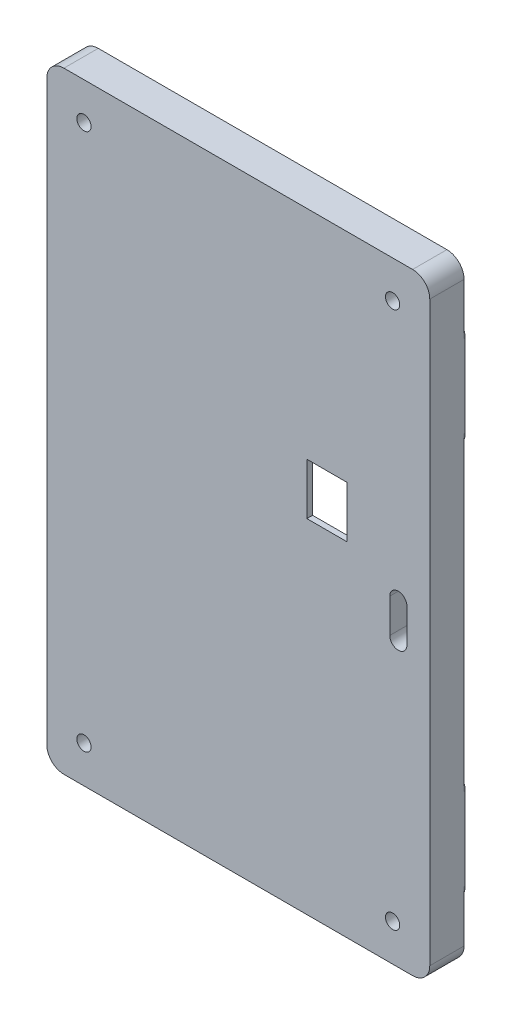
SolidWorks part; units mm, degrees
ref_plane "Přední rovina" through (0, 0, 0) normal (0, 0, 1) x (1, 0, 0)
ref_plane "Horní rovina" through (0, 0, 0) normal (0, 1, 0) x (1, 0, 0)
ref_plane "Pravá rovina" through (0, 0, 0) normal (1, 0, 0) x (0, 0, -1)
sketch "Skica1" plane through (0, 0, 0) normal (0, 0, 1) x (1, 0, 0)
  line L1 (0, 0) -> (67, 0)
  line L2 (0, 0) -> (0, 107)
  line L3 (0, 107) -> (67, 107)
  line L4 (67, 0) -> (67, 107)
  dimension "D1" = 67
  dimension "D2" = 107
extrude "Přidat vysunutím1" add sketch "Skica1" along normal blind 6
fillet "Zaoblit1" radius 3 4 edges at (67, 0, 3) (0, 0, 3) (0, 107, 3) (67, 107, 3)
sketch "Skica2" plane through (0, 0, 0) normal (0, 0, -1) x (-1, 0, 0)
  line L0 (-60.5, 100.5) -> (-6.5, 100.5) construction
  line L1 (-64, 107) -> (-3, 107) construction
  line L2 (-60.5, 100.5) -> (-60.5, 6.5) construction
  line L3 (-67, 3) -> (-67, 104) construction
  circle A0 centre (-6.5, 100.5) radius 1.25
  circle A1 centre (-60.5, 100.5) radius 1.25
  circle A2 centre (-6.5, 6.5) radius 1.25
  circle A3 centre (-60.5, 6.5) radius 1.25
  point P8 (-33.5, 100.5)
  point P11 (-33.5, 107)
  point P12 (-60.5, 53.5)
  point P15 (-67, 53.5)
  dimension "D3" = 2.5
  dimension "D4" = 2.5
  dimension "D5" = 2.5
  dimension "D6" = 2.5
  dimension "D1" = 94
  dimension "D2" = 54
extrude "Odebrat vysunutím1" cut sketch "Skica2" against normal through all
chamfer "Zkosení1" distance 1.25 angle 45 4 edges at (5.25, 6.5, 0) (59.25, 6.5, 0) (59.25, 100.5, 0) (5.25, 100.5, 0)
sketch "Skica4" plane through (0, 0, 0) normal (0, 0, -1) x (-1, 0, 0)
  line L0 (-61.5, 55.5) -> (-61.5, 49.55) construction
  line L1 (-52.5, 69) -> (-45.5, 69)
  line L2 (-52.5, 69) -> (-52.5, 60)
  line L3 (-52.5, 60) -> (-45.5, 60)
  line L4 (-45.5, 69) -> (-45.5, 60)
  line L5 (-60, 55.5) -> (-60, 49.55)
  line L6 (-63, 55.5) -> (-63, 49.55)
  line L7 (-67, 3) -> (-67, 104) construction
  line L8 (-64, 107) -> (-3, 107) construction
  arc A2 (-60, 55.5) -> (-63, 55.5) centre (-61.5, 55.5) ccw
  arc A3 (-63, 49.55) -> (-60, 49.55) centre (-61.5, 49.55) ccw
  point P6 (-61.5, 52.525)
  dimension "D1" = 7
  dimension "D3" = 5.95
  dimension "D4" = 1.5
  dimension "D2" = 9
  dimension "D5" = 5.5
  dimension "D6" = 51.5
  dimension "D7" = 14.5
  dimension "D8" = 38
extrude "Odebrat vysunutím2" cut sketch "Skica4" against normal through all contours L1 L4 L3 L2 | L5 A3 L6 A2
sketch "Skica7" plane through (0, 0, 0) normal (0, 0, -1) x (-1, 0, 0)
  line L0 (-67, 3) -> (-67, 104) construction
  line L1 (-59, 97) -> (-8, 97)
  line L2 (-59, 97) -> (-59, 10)
  line L3 (-59, 10) -> (-8, 10)
  line L4 (-8, 97) -> (-8, 10)
  line L6 (0, 104) -> (0, 3) construction
  line L7 (-64, 107) -> (-3, 107) construction
  line L8 (-3, 0) -> (-64, 0) construction
  dimension "D1" = 8
  dimension "D2" = 8
  dimension "D3" = 10
  dimension "D4" = 10
extrude "Odebrat vysunutím3" cut sketch "Skica7" against normal blind 5
sketch "Skica8" plane through (0, 0, 5) normal (0, 0, -1) x (-1, 0, 0)
  line L0 (-8, 97) -> (-59, 97) construction
  line L1 (-53.9, 97) -> (-48.9, 97)
  line L2 (-53.9, 97) -> (-53.9, 92)
  line L3 (-53.9, 92) -> (-48.9, 92)
  line L4 (-48.9, 97) -> (-48.9, 92)
  line L5 (-59, 97) -> (-59, 10) construction
  line L6 (-18.1, 97) -> (-13.1, 97)
  line L7 (-18.1, 97) -> (-18.1, 92)
  line L8 (-18.1, 92) -> (-13.1, 92)
  line L9 (-13.1, 97) -> (-13.1, 92)
  line L10 (-8, 10) -> (-8, 97) construction
  dimension "D1" = 5
  dimension "D2" = 5.1
  dimension "D3" = 5.1
  dimension "D4" = 5
  dimension "D5" = 5
extrude "Přidat vysunutím2" add sketch "Skica8" along normal blind 5
sketch "Skica9" plane through (48.9, 0, 0) normal (-1, 0, 0) x (0, 0, 1)
  line L0 (5, 92) -> (0, 97) construction
  circle A0 centre (2.5, 94.5) radius 0.95
  dimension "D1" = 1.9
extrude "Odebrat vysunutím4" cut sketch "Skica9" against normal blind 14
sketch "Skica10" plane through (18.1, 0, 0) normal (1, 0, 0) x (0, 0, -1)
  line L0 (-5, 97) -> (0, 92) construction
  circle A0 centre (-2.5, 94.5) radius 0.95
  dimension "D1" = 1.9
extrude "Odebrat vysunutím5" cut sketch "Skica10" against normal blind 14
sketch "Skica11" plane through (0, 0, 0) normal (0, 0, -1) x (-1, 0, 0)
  line L0 (-3.1, 95) -> (-3.1, 80.6) construction
  line L1 (0, 95) -> (0, 80.6)
  line L2 (-6.2, 95) -> (-6.2, 80.6)
  line L3 (-3.1, 26.4) -> (-3.1, 12) construction
  line L4 (0, 26.4) -> (0, 12)
  line L5 (-6.2, 26.4) -> (-6.2, 12)
  line L6 (-63.9, 95) -> (-63.9, 80.6) construction
  line L7 (-60.8, 95) -> (-60.8, 80.6)
  line L8 (-67, 95) -> (-67, 80.6)
  line L9 (-63.9, 26.4) -> (-63.9, 12) construction
  line L10 (-60.8, 26.4) -> (-60.8, 12)
  line L11 (-67, 26.4) -> (-67, 12)
  line L12 (-67, 3) -> (-67, 104) construction
  line L13 (0, 104) -> (0, 3) construction
  line L14 (-64, 107) -> (-3, 107) construction
  line L15 (-3, 0) -> (-64, 0) construction
  arc A0 (0, 95) -> (-6.2, 95) centre (-3.1, 95) ccw
  arc A1 (-6.2, 80.6) -> (0, 80.6) centre (-3.1, 80.6) ccw
  arc A2 (0, 26.4) -> (-6.2, 26.4) centre (-3.1, 26.4) ccw
  arc A3 (-6.2, 12) -> (0, 12) centre (-3.1, 12) ccw
  arc A4 (-60.8, 95) -> (-67, 95) centre (-63.9, 95) ccw
  arc A5 (-67, 80.6) -> (-60.8, 80.6) centre (-63.9, 80.6) ccw
  arc A6 (-60.8, 26.4) -> (-67, 26.4) centre (-63.9, 26.4) ccw
  arc A7 (-67, 12) -> (-60.8, 12) centre (-63.9, 12) ccw
  point P2 (-3.1, 87.8)
  point P7 (-3.1, 19.2)
  point P14 (-63.9, 87.8)
  point P21 (-63.9, 19.2)
  point P28 (0, 19.2)
  point P29 (0, 0)
  point P30 (0, 0)
  point P31 (0, 0)
  point P32 (0, 0)
  dimension "D5" = 14.4
  dimension "D1" = 6.2
  dimension "D2" = 6.2
  dimension "D3" = 6.2
  dimension "D4" = 6.2
  dimension "D6" = 14.4
  dimension "D7" = 12
  dimension "D8" = 12
extrude "Přidat vysunutím3" add sketch "Skica11" along normal blind 0.2
